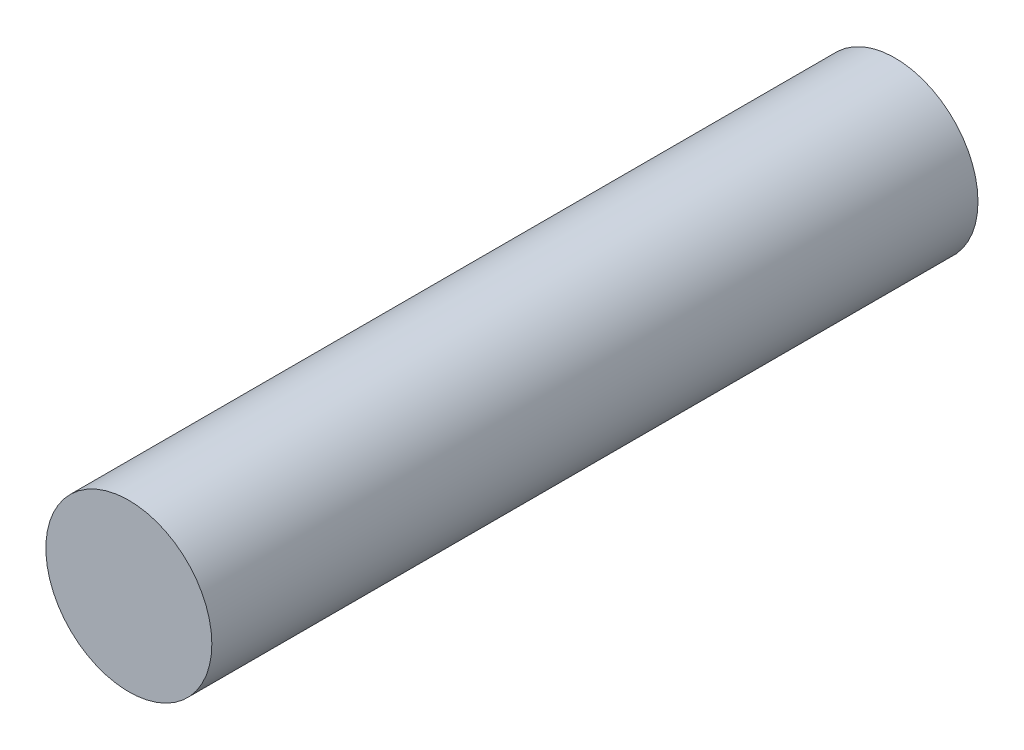
SolidWorks part; units mm, degrees
ref_plane "Front Plane" through (0, 0, 0) normal (0, 0, 1) x (1, 0, 0)
ref_plane "Top Plane" through (0, 0, 0) normal (0, 1, 0) x (1, 0, 0)
ref_plane "Right Plane" through (0, 0, 0) normal (1, 0, 0) x (0, 0, -1)
sketch "Sketch1" plane through (0, 0, 0) normal (0, 0, 1) x (1, 0, 0)
  circle A0 centre (0, 0) radius 3.25
  dimension "D1" = 6.5
extrude "Boss-Extrude1" add sketch "Sketch1" against normal blind 30
